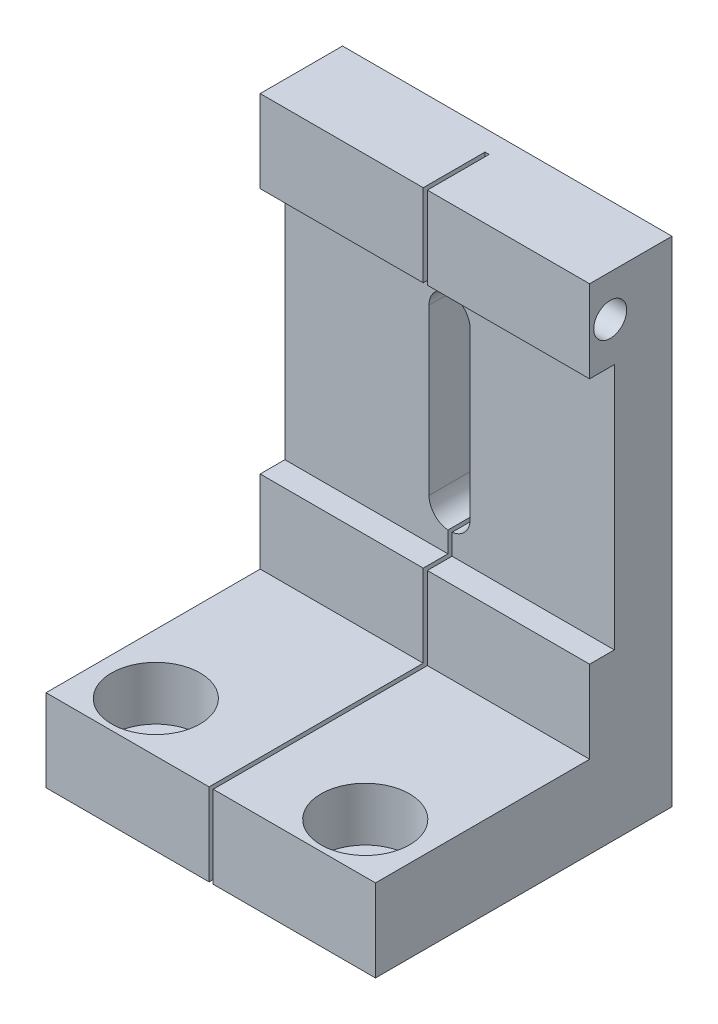
SolidWorks part; units mm, degrees
ref_plane "Front Plane" through (0, 0, 0) normal (0, 0, 1) x (1, 0, 0)
ref_plane "Top Plane" through (0, 0, 0) normal (0, 1, 0) x (1, 0, 0)
ref_plane "Right Plane" through (0, 0, 0) normal (1, 0, 0) x (0, 0, -1)
sketch "Sketch1" plane through (0, 0, 0) normal (0, 0, 1) x (1, 0, 0)
  line L1 (0, 0) -> (-40, 0)
  line L2 (0, 0) -> (0, -60)
  line L3 (0, -60) -> (-40, -60)
  line L4 (-40, 0) -> (-40, -60)
  dimension "D1" = 40
  dimension "D2" = 60
extrude "Boss-Extrude1" add sketch "Sketch1" along normal blind 10
sketch "Sketch2" plane through (0, 0, 10) normal (0, 0, 1) x (1, 0, 0)
  line L0 (-20, -15) -> (-20, -35) construction
  line L1 (-17.5, -15) -> (-17.5, -35)
  line L2 (-22.5, -15) -> (-22.5, -35)
  line L4 (-40, -60) -> (0, -60) construction
  line L5 (0, 0) -> (-40, 0) construction
  line L6 (-20, 0) -> (-20, -5.6142) construction
  arc A0 (-17.5, -15) -> (-22.5, -15) centre (-20, -15) ccw
  arc A1 (-22.5, -35) -> (-17.5, -35) centre (-20, -35) ccw
  point P2 (-20, -25)
  dimension "D1" = 5
  dimension "D2" = 20
  dimension "D4" = 35
extrude "Cut-Extrude1" cut sketch "Sketch2" against normal through all
sketch "Sketch5" plane through (0, 0, 0) normal (1, 0, 0) x (0, 0, -1)
  line L0 (-7, -10) -> (-10, -10)
  line L1 (-10, -60) -> (-10, 0) construction
  line L2 (-7, -10) -> (-7, -40)
  line L3 (-10, -60) -> (0, -60) construction
  line L4 (-7, -40) -> (-10, -40)
  line L7 (-10, -10) -> (-10, -40)
  dimension "D1" = 3
  dimension "D4" = 30
  dimension "D5" = 20
extrude "Cut-Extrude4" cut sketch "Sketch5" against normal through all
sketch "Sketch6" plane through (0, 0, 10) normal (0, 0, 1) x (1, 0, 0)
  line L0 (-40, -40) -> (-40, -60) construction
  line L1 (0, -60) -> (-40, -60)
  line L2 (0, -60) -> (0, -50)
  line L3 (0, -50) -> (-40, -50)
  line L4 (-40, -60) -> (-40, -50)
  dimension "D1" = 10
extrude "Boss-Extrude2" add sketch "Sketch6" along normal blind 26
sketch "Sketch7" plane through (0, -50, 0) normal (0, 1, 0) x (1, 0, 0)
  line L3 (-40, -36) -> (-40, -10) construction
  circle A0 centre (-4.0875, -15.1829) radius 2
  circle A1 centre (-35.875, -15.1829) radius 2
  dimension "D1" = 4
  dimension "D2" = 4
  dimension "D3" = 4.125
  dimension "D5" = 31.7875
extrude "Cut-Extrude5" [suppressed] cut sketch "Sketch7" against normal blind 40
sketch "Sketch8" plane through (0, 0, 0) normal (0, 1, 0) x (1, 0, 0)
  line L0 (0, -10) -> (-40, -10) construction
  line L2 (-20.2, -36) -> (-19.7, -36)
  line L5 (-20.2, -36) -> (-20.2, -2.5)
  line L7 (0, -36) -> (-40, -36) construction
  line L9 (-20.2, -2.5) -> (-19.7, -2.5)
  line L10 (-19.7, -36) -> (-19.7, -2.5)
  line L11 (-22.5, 0) -> (-22.5, -7) construction
  dimension "D1" = 0.5
  dimension "D2" = 2.3
  dimension "D3" = 7.5
extrude "Cut-Extrude7" cut sketch "Sketch8" against normal up to surface (60 mm away) up to face at (-20, -60, 18)
sketch "Sketch9" plane through (0, -60, 0) normal (0, -1, 0) x (1, 0, 0)
  line L3 (0, 36) -> (0, 0) construction
  line L5 (-40, 7) -> (-20.2, 7) construction
  circle A0 centre (-32.73, 5) radius 2
  circle A1 centre (-7.3, 5) radius 2
  dimension "D1" = 4
  dimension "D3" = 7.3
  dimension "D4" = 4
  dimension "D2" = 25.43
extrude "Cut-Extrude9" [suppressed] cut sketch "Sketch9" against normal blind 15
sketch "Sketch10" plane through (0, 0, 0) normal (1, 0, 0) x (0, 0, -1)
  line L1 (-10, 0) -> (0, 0) construction
  line L2 (-10, -10) -> (-10, 0) construction
  circle A0 centre (-7.5, -5) radius 2
  dimension "D1" = 4
  dimension "D2" = 5
  dimension "D3" = 2.5
extrude "Cut-Extrude10" cut sketch "Sketch10" against normal blind 30
sketch "Sketch12" plane through (0, -60, 0) normal (0, -1, 0) x (1, 0, 0)
  line L0 (-32.73, 29.94) -> (-32.73, 4.51) construction
  line L1 (-32.73, 4.51) -> (-7.3, 4.51) construction
  line L2 (-7.3, 4.51) -> (-7.3, 29.94) construction
  line L3 (-7.3, 29.94) -> (-32.73, 29.94) construction
  line L4 (-40, 7) -> (-20.2, 7) construction
  line L6 (0, 36) -> (0, 0) construction
  line L10 (-19.7, 36) -> (0, 36) construction
  line L11 (-40, 0) -> (-40, 36) construction
  circle A0 centre (-7.3, 29.94) radius 3.4
  circle A1 centre (-32.73, 29.94) radius 3.4
  circle A2 centre (-32.73, 4.51) radius 2.49
  circle A3 centre (-7.3, 4.51) radius 2.49
  circle A4 centre (-7.3, 29.94) radius 5.375 construction
  circle A5 centre (-32.73, 4.54) radius 3.4 [skipped]
  circle A6 centre (-7.3, 4.54) radius 3.4 [skipped]
  dimension "D1" = 6.8
  dimension "D2" = 2
  dimension "D3" = 2
  dimension "D4" = 10.75
  dimension "D6" = 7.3
  dimension "D7" = 25.43
  dimension "D8" = 4.98
  dimension "D9" = 25.43
  dimension "D11" = 6.06
  dimension "D5" = 2
  dimension "D12" = 7.27
extrude "Cut-Extrude13" cut sketch "Sketch12" against normal up to surface (10 mm away) up to face at (-9.85, -50, 23)
sketch "Sketch14" plane through (0, -50, 0) normal (0, 1, 0) x (1, 0, 0)
  line L0 (-32.73, -29.94) -> (18.13, -29.94) construction
  circle A0 centre (-32.73, -29.94) radius 5.375
  circle A1 centre (-7.3, -29.94) radius 5.375
  dimension "D1" = 10.75
  dimension "D3" = 25.43
  dimension "D2" = 2
extrude "Cut-Extrude14" cut sketch "Sketch14" against normal blind 6.5
equation "\"inch\"= 25.43"
equation "\"D5@Sketch7\"=\"inch\"*1.25"
equation "\"D2@Sketch9\"=\"inch\""
equation "\"D7@Sketch12\"=\"inch\""
equation "\"D9@Sketch12\"=\"inch\""
equation "\"D3@Sketch14\"=\"inch\""
